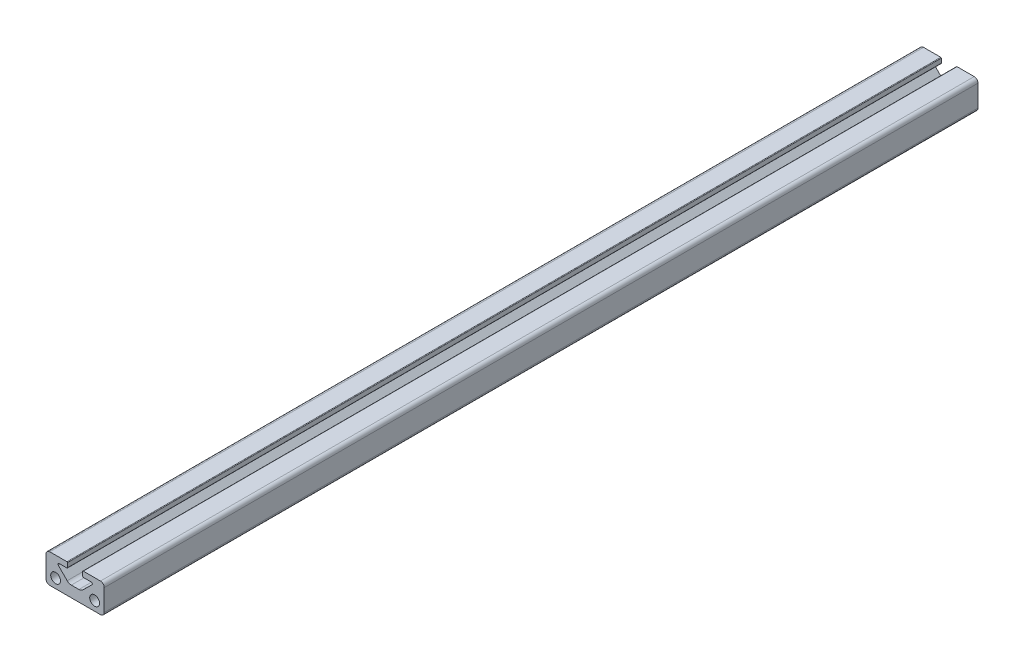
SolidWorks part; units mm, degrees
other "Imported1" parameters "D1"=381, "Length"=381
ref_plane "Front" through (0, 0, 0) normal (0, 0, 1) x (1, 0, 0)
ref_plane "Top" through (0, 0, 0) normal (0, 1, 0) x (1, 0, 0)
ref_plane "Right" through (0, 0, 0) normal (1, 0, 0) x (0, 0, -1)
sketch "Sketch1" plane through (0, 0, 0) normal (0, 0, 1) x (1, 0, 0)
  line L0 (-3.302, 12.7) -> (3.302, 12.7) construction
  line L1 (-7.493, 9.8209) -> (7.493, 9.8209) construction
  line L2 (-11.049, 12.7) -> (-3.302, 12.7)
  line L3 (3.302, 12.7) -> (11.049, 12.7)
  line L4 (11.049, 0) -> (-11.049, 0)
  line L5 (-8.509, 4.064) -> (8.509, 4.064) construction
  line L6 (-3.302, 12.7) -> (-3.302, 10.3289)
  line L7 (3.302, 12.7) -> (3.302, 10.3289)
  line L28 (-12.7, 11.049) -> (-12.7, 1.651)
  line L32 (12.7, 1.651) -> (12.7, 11.049)
  line L35 (3.302, 10.3289) -> (6.985, 10.3289)
  line L36 (7.3442, 9.4617) -> (3.4525, 5.5699)
  line L37 (1.6565, 4.826) -> (-1.6565, 4.826)
  line L38 (-3.4525, 5.5699) -> (-7.3442, 9.4617)
  line L39 (-6.985, 10.3289) -> (-3.302, 10.3289)
  circle A0 centre (-8.509, 4.064) radius 2.1463
  circle A1 centre (8.509, 4.064) radius 2.1463
  arc A36 (-12.7, 1.651) -> (-11.049, 0) centre (-11.049, 1.651) ccw
  arc A41 (11.049, 0) -> (12.7, 1.651) centre (11.049, 1.651) ccw
  arc A42 (12.7, 11.049) -> (11.049, 12.7) centre (11.049, 11.049) ccw
  arc A46 (7.3442, 9.4617) -> (6.985, 10.3289) centre (6.985, 9.8209) ccw
  arc A47 (1.6565, 4.826) -> (3.4525, 5.5699) centre (1.6565, 7.366) ccw
  arc A48 (-3.4525, 5.5699) -> (-1.6565, 4.826) centre (-1.6565, 7.366) ccw
  arc A49 (-6.985, 10.3289) -> (-7.3442, 9.4617) centre (-6.985, 9.8209) ccw
  arc A53 (-11.049, 12.7) -> (-12.7, 11.049) centre (-11.049, 11.049) ccw
  point P5 (0, 4.064)
  point P8 (0, 0)
  point P10 (0, 4.826)
  point P11 (0, 9.8209)
  point P13 (0, 12.7)
  dimension "D6" = 1.651
  dimension "D7" = 0.508
  dimension "D8" = 8.636
  dimension "D9" = 4.2926
  dimension "D12" = 2.54
  dimension "D1" = 6.604
  dimension "D2" = 14.986
  dimension "D3" = 17.018
  dimension "D4" = 25.4
  dimension "D5" = 12.7
  dimension "D10" = 7.874
  dimension "D11" = 2.3711
  dimension "D13" = 45
sketch "Sketch2" plane through (0, 0, 0) normal (1, 0, 0) x (0, 0, -1)
  line L0 (190.5, 0) -> (-190.5, 0) construction
  point P4 (0, 0)
sketch "Sketch3" plane through (0, 0, 0) normal (0, 0, 1) x (1, 0, 0)
  line L0 (-11.049, 12.7) -> (-3.302, 12.7) construction
  line L1 (-3.302, 12.7) -> (-3.302, 10.3289) construction
  line L2 (-6.985, 10.3289) -> (-3.302, 10.3289) construction
  line L3 (-3.4525, 5.5699) -> (-7.3442, 9.4617) construction
  line L4 (1.6565, 4.826) -> (-1.6565, 4.826) construction
  line L5 (7.3442, 9.4617) -> (3.4525, 5.5699) construction
  line L6 (3.302, 10.3289) -> (6.985, 10.3289) construction
  line L7 (3.302, 12.7) -> (3.302, 10.3289) construction
  line L8 (3.302, 12.7) -> (11.049, 12.7) construction
  line L9 (12.7, 1.651) -> (12.7, 11.049) construction
  line L10 (11.049, 0) -> (-11.049, 0) construction
  line L11 (-12.7, 11.049) -> (-12.7, 1.651) construction
  line L12 (-11.049, 12.7) -> (-3.302, 12.7)
  line L13 (-3.302, 12.7) -> (-3.302, 10.3289)
  line L14 (-6.985, 10.3289) -> (-3.302, 10.3289)
  line L15 (-3.4525, 5.5699) -> (-7.3442, 9.4617)
  line L16 (1.6565, 4.826) -> (-1.6565, 4.826)
  line L17 (7.3442, 9.4617) -> (3.4525, 5.5699)
  line L18 (3.302, 10.3289) -> (6.985, 10.3289)
  line L19 (3.302, 12.7) -> (3.302, 10.3289)
  line L20 (3.302, 12.7) -> (11.049, 12.7)
  line L21 (12.7, 1.651) -> (12.7, 11.049)
  line L22 (11.049, 0) -> (-11.049, 0)
  line L23 (-12.7, 11.049) -> (-12.7, 1.651)
  circle A0 centre (8.509, 4.064) radius 2.1463 construction
  circle A1 centre (-8.509, 4.064) radius 2.1463 construction
  arc A2 (-6.985, 10.3289) -> (-7.3442, 9.4617) centre (-6.985, 9.8209) ccw construction
  arc A3 (-3.4525, 5.5699) -> (-1.6565, 4.826) centre (-1.6565, 7.366) ccw construction
  arc A4 (1.6565, 4.826) -> (3.4525, 5.5699) centre (1.6565, 7.366) ccw construction
  arc A5 (7.3442, 9.4617) -> (6.985, 10.3289) centre (6.985, 9.8209) ccw construction
  arc A6 (12.7, 11.049) -> (11.049, 12.7) centre (11.049, 11.049) ccw construction
  arc A7 (11.049, 0) -> (12.7, 1.651) centre (11.049, 1.651) ccw construction
  arc A8 (-12.7, 1.651) -> (-11.049, 0) centre (-11.049, 1.651) ccw construction
  arc A9 (-11.049, 12.7) -> (-12.7, 11.049) centre (-11.049, 11.049) ccw construction
  circle A10 centre (8.509, 4.064) radius 2.1463
  circle A11 centre (-8.509, 4.064) radius 2.1463
  arc A12 (-6.985, 10.3289) -> (-7.3442, 9.4617) centre (-6.985, 9.8209) ccw
  arc A13 (-3.4525, 5.5699) -> (-1.6565, 4.826) centre (-1.6565, 7.366) ccw
  arc A14 (1.6565, 4.826) -> (3.4525, 5.5699) centre (1.6565, 7.366) ccw
  arc A15 (7.3442, 9.4617) -> (6.985, 10.3289) centre (6.985, 9.8209) ccw
  arc A16 (12.7, 11.049) -> (11.049, 12.7) centre (11.049, 11.049) ccw
  arc A17 (11.049, 0) -> (12.7, 1.651) centre (11.049, 1.651) ccw
  arc A18 (-12.7, 1.651) -> (-11.049, 0) centre (-11.049, 1.651) ccw
  arc A19 (-11.049, 12.7) -> (-12.7, 11.049) centre (-11.049, 11.049) ccw
extrude "Boss-Extrude1" add sketch "Sketch3" along normal mid plane 381
fillet "Fillet1" radius 0.254 4 edges at (3.302, 10.3289, 0) (3.302, 12.7, 0) (-3.302, 10.3289, 0) (-3.302, 12.7, 0)
equation "\"D1@Boss-Extrude1\"=\"Length@Sketch2\""
